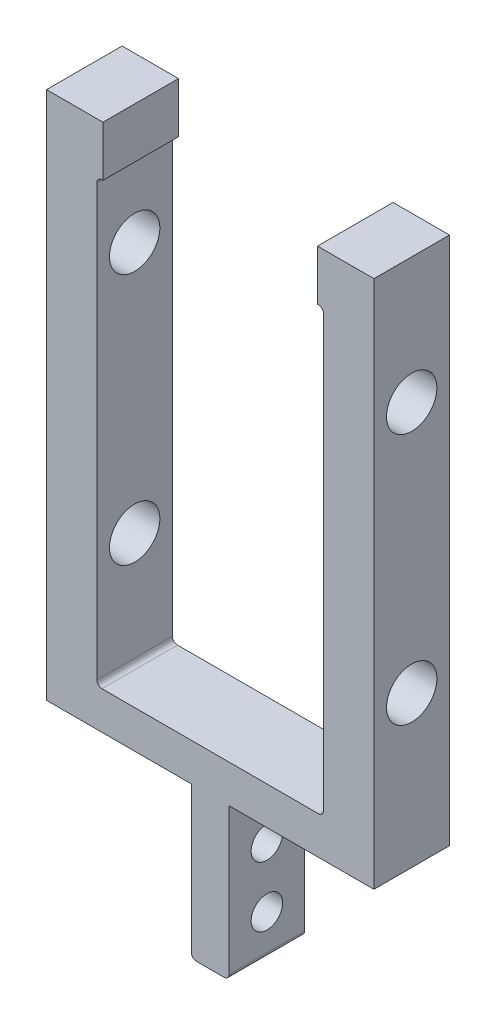
SolidWorks part; units mm, degrees
material "6061 Alloy"
ref_plane "Front Plane" through (0, 0, 0) normal (0, 0, 1) x (1, 0, 0)
ref_plane "Top Plane" through (0, 0, 0) normal (0, 1, 0) x (1, 0, 0)
ref_plane "Right Plane" through (0, 0, 0) normal (1, 0, 0) x (0, 0, -1)
sketch "Sketch1" plane through (0, 0, 0) normal (0, 0, 1) x (1, 0, 0)
  line L7 (4.7625, 0) -> (-4.7625, 0)
  line L13 (-4.7625, 0) -> (-4.7625, 38.1)
  line L14 (-4.7625, 38.1) -> (-41.275, 38.1)
  line L15 (-41.275, 38.1) -> (-41.275, 171.45)
  line L17 (-28.575, 158.75) -> (-28.575, 47.625)
  line L18 (-28.575, 47.625) -> (28.575, 47.625)
  line L19 (0, 47.625) -> (0, 0) construction
  line L20 (28.575, 158.75) -> (28.575, 47.625)
  line L22 (41.275, 38.1) -> (41.275, 171.45)
  line L23 (4.7625, 38.1) -> (41.275, 38.1)
  line L24 (4.7625, 0) -> (4.7625, 38.1)
  line L26 (41.275, 171.45) -> (27.051, 171.45)
  line L29 (28.575, 158.75) -> (27.051, 158.75)
  line L30 (27.051, 171.45) -> (27.051, 158.75)
  line L31 (-27.051, 158.75) -> (-27.051, 171.45)
  line L32 (-27.051, 158.75) -> (-28.575, 158.75)
  line L33 (27.051, 158.75) -> (-27.051, 158.75) construction
  line L34 (-27.051, 171.45) -> (-41.275, 171.45)
  line L35 (27.051, 171.45) -> (-27.051, 171.45) construction
  line L36 (0, -10.4775) -> (0, 10.4775) construction
  point P12 (0, 47.625)
  point P17 (0, 0)
  point P21 (-23.3595, 171.45)
  point P22 (22.9217, 158.75)
  point P24 (0, 171.45)
  dimension "D1" = 9.525
  dimension "D2" = 57.15
  dimension "D3" = 38.1
  dimension "D4" = 82.55
  dimension "D5" = 9.525
  dimension "D6" = 12.7
  dimension "D7" = 54.102
  dimension "D8" = 133.35
extrude "Boss-Extrude1" add sketch "Sketch1" along normal mid plane 19.05
sketch "Sketch2" plane through (-41.275, 0, 0) normal (-1, 0, 0) x (0, 0, 1)
  line L0 (-26.0251, 0) -> (40.3307, 0) construction
  line L1 (0, 127) -> (0, 0) construction
  circle A0 centre (0, 76.2) radius 6.35
  circle A1 centre (0, 139.7) radius 6.35
  dimension "D2" = 12.7
  dimension "D1" = 12.7
  dimension "D4" = 63.5
  dimension "D3" = 76.2
extrude "Cut-Extrude1" cut sketch "Sketch2" against normal through all
fillet "Fillet1" radius 1.27 6 edges at (-28.575, 47.625, 0) (28.575, 47.625, 0) (28.575, 158.75, 0) (-4.7625, 0, 0) (4.7625, 0, 0) (-28.575, 158.75, 0)
hole_wizard "Hole1" positions "Sketch15" profile "Sketch16" legacy end condition through all
sketch "Sketch15" plane through (4.7625, 0, 0) normal (-1, 0, 0) x (0, 0, 1)
  line L0 (0, -45.4025) -> (0, 45.4025) construction
  line L1 (-9.525, 0) -> (9.525, 0) construction
  point P0 (0, 25.4)
  point P3 (0, 10.16)
  point P8 (0, 0)
  point P9 (0.3341, -8.89)
  point P13 (0, 0)
  point P14 (0, 0)
  point P15 (0, 0)
  point P16 (0, 0)
  point P17 (0, 5.0336)
  point P18 (0, 0)
  dimension "D1" = 10.16
  dimension "D2" = 15.24
sketch "Sketch16" plane through (4.7625, 25.4, 0) normal (0, 1, 0) x (0, 0, -1)
  line L0 (0, 0) -> (0, 48.4245)
  line L1 (0, 48.4245) -> (3.9726, 46.0375)
  line L2 (3.9726, 46.0375) -> (3.9726, 0)
  line L4 (3.9726, 0) -> (0, 0)
  line L6 (0, 48.4245) -> (-3.9726, 46.0375) construction
  line L7 (0, -4.2442) -> (0, 117.3081) construction
  dimension "Diameter" = 7.9451
  dimension "Depth" = 46.0375
  dimension "Drill Angle" = 118
equation "\"BoomDistance\"=2.5"
equation "\"D4@Sketch2\"=\"BoomDistance\""
